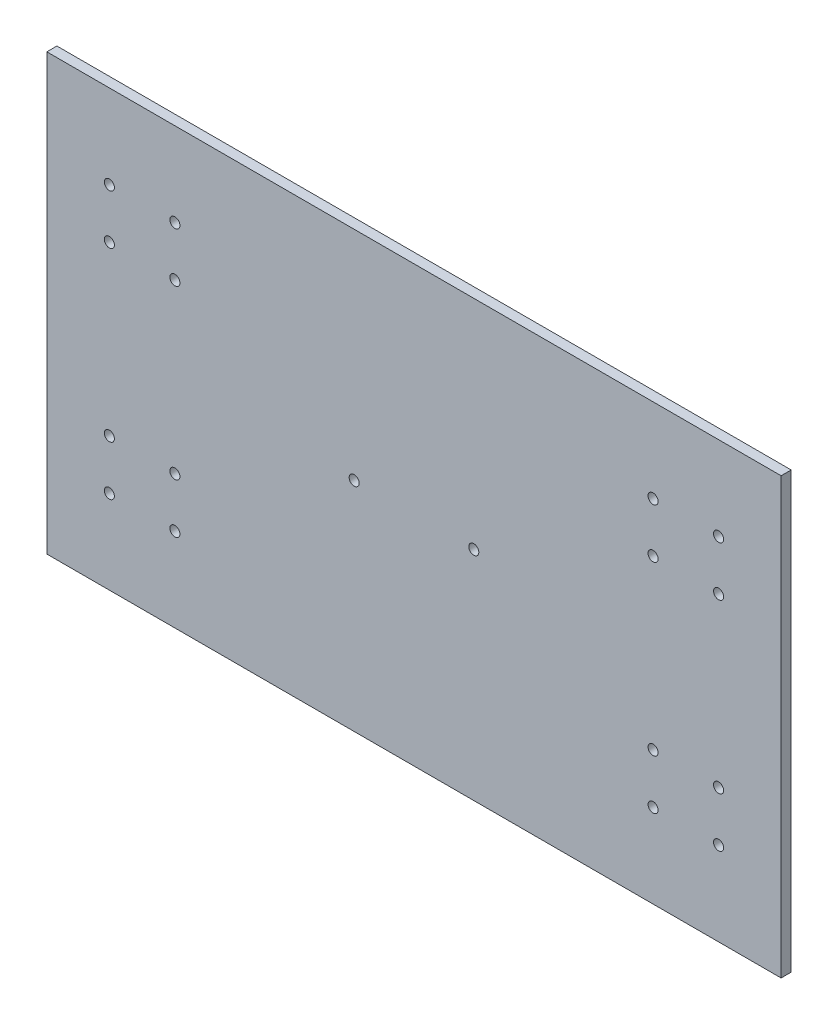
SolidWorks part; units mm, degrees
ref_plane "Alzado" through (0, 0, 0) normal (0, 0, 1) x (1, 0, 0)
ref_plane "Planta" through (0, 0, 0) normal (0, 1, 0) x (1, 0, 0)
ref_plane "Vista lateral" through (0, 0, 0) normal (1, 0, 0) x (0, 0, -1)
sketch "Sketch1" plane through (0, 0, 0) normal (0, 0, 1) x (1, 0, 0)
  line L0 (270.1, 160) -> (270.1, 0)
  line L1 (270.1, 160) -> (0, 160)
  line L2 (270.1, 0) -> (0, 0)
  line L3 (0, 160) -> (0, 0)
  line L4 (23, 51) -> (-40.1501, 51) construction
  line L5 (23, 29) -> (-41.1836, 29) construction
  line L6 (48.95, 49.15) -> (48.95, 14.2835) construction
  line L7 (21.15, 49.15) -> (21.15, 13.6529) construction
  line L8 (23, 49.15) -> (47.1, 30.85) construction
  line L9 (23, 30.85) -> (47.1, 49.15) construction
  line L10 (135.05, 40) -> (135.05, 23.6262) construction
  line L11 (270.1, 80) -> (186.3601, 80) construction
  line L12 (186.3601, 60) -> (107.7684, 60) construction
  circle A0 centre (6, 154) radius 1.85
  circle A1 centre (6, 6) radius 1.85
  circle A2 centre (264.1, 154) radius 1.85
  circle A3 centre (264.1, 6) radius 1.85
  circle A4 centre (113.05, 40) radius 1.85
  circle A5 centre (157.05, 40) radius 1.85
  circle A6 centre (23, 49.15) radius 1.85
  circle A7 centre (47.1, 49.15) radius 1.85
  circle A8 centre (23, 30.85) radius 1.85
  circle A9 centre (47.1, 30.85) radius 1.85
  circle A10 centre (223, 30.85) radius 1.85
  circle A11 centre (223, 49.15) radius 1.85
  circle A12 centre (247.1, 49.15) radius 1.85
  circle A13 centre (247.1, 30.85) radius 1.85
  circle A14 centre (23, 129.15) radius 1.85
  circle A15 centre (23, 110.85) radius 1.85
  circle A16 centre (47.1, 110.85) radius 1.85
  circle A17 centre (47.1, 129.15) radius 1.85
  circle A18 centre (223, 110.85) radius 1.85
  circle A19 centre (223, 129.15) radius 1.85
  circle A20 centre (247.1, 129.15) radius 1.85
  circle A21 centre (247.1, 110.85) radius 1.85
  circle A22 centre (113.05, 80) radius 1.85
  circle A23 centre (157.05, 80) radius 1.85
  circle A24 centre (47.1, 129.15) radius 1.85
  circle A25 centre (47.1, 110.85) radius 1.85
  circle A26 centre (23, 110.85) radius 1.85
  circle A27 centre (23, 129.15) radius 1.85
  circle A28 centre (157.05, 80) radius 1.85
  circle A29 centre (113.05, 80) radius 1.85
  circle A30 centre (223, 110.85) radius 1.85
  circle A31 centre (223, 129.15) radius 1.85
  circle A32 centre (247.1, 110.85) radius 1.85
  circle A33 centre (247.1, 129.15) radius 1.85
  circle A34 centre (247.1, 49.15) radius 1.85
  circle A35 centre (223, 49.15) radius 1.85
  circle A36 centre (223, 30.85) radius 1.85
  circle A37 centre (247.1, 30.85) radius 1.85
  circle A38 centre (47.1, 49.15) radius 1.85
  circle A39 centre (47.1, 30.85) radius 1.85
  circle A40 centre (23, 30.85) radius 1.85
  circle A41 centre (23, 49.15) radius 1.85
  point P32 (35.05, 40)
  point P35 (135.05, 40)
  dimension "D1" = 3.7
  dimension "D21" = 3.7
  dimension "D2" = 22
  dimension "D3" = 27.8
  dimension "D4" = 44
  dimension "D5" = 22
  dimension "D6" = 100
  dimension "D7" = 160
  dimension "D8" = 6
  dimension "D9" = 6
  dimension "D10" = 6
  dimension "D11" = 6
  dimension "D12" = 6
  dimension "D13" = 6
  dimension "D14" = 6
  dimension "D15" = 6
  dimension "D16" = 17
  dimension "D17" = 17
  dimension "D18" = 40
  dimension "D19" = 100
  dimension "D20" = 20
extrude "Boss-Extrude1" add sketch "Sketch1" along normal blind 3.7 contours L1 L3 L2 L0 A22 A21 A20 A19 A18 A16 A14 A12 A10 A9 A8 A7 A6 A5 A4 A3 A2 A1 A0 A11 A13 A15 A17
